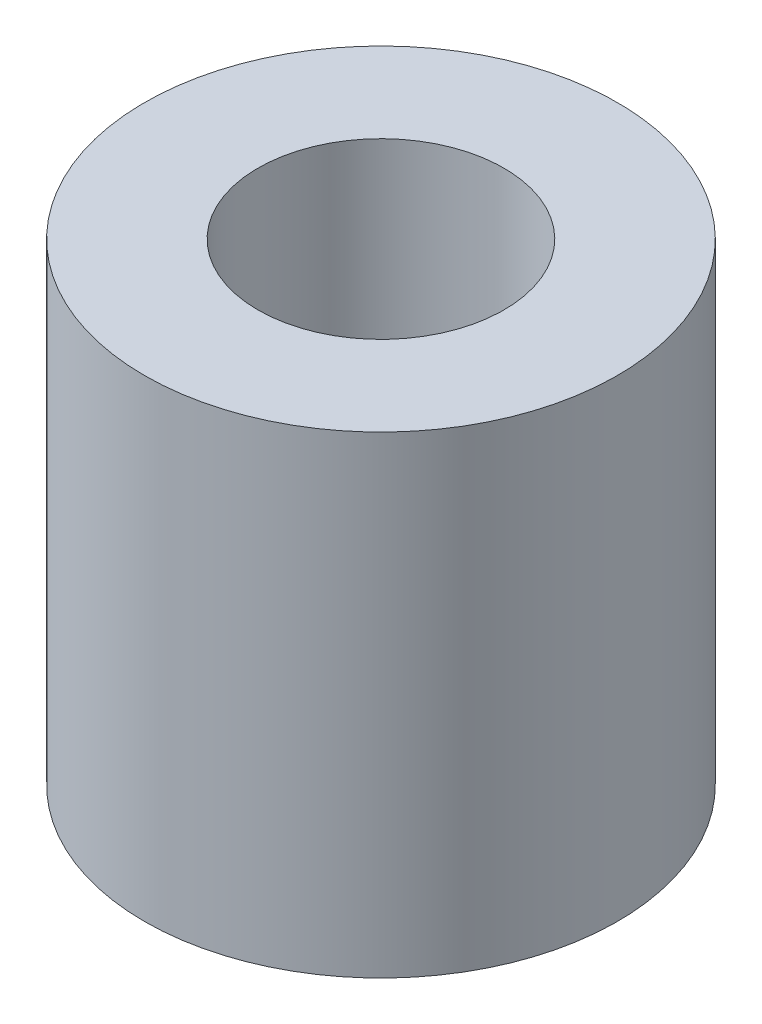
SolidWorks part; units mm, degrees
ref_plane "Front" through (0, 0, 0) normal (0, 0, 1) x (1, 0, 0)
ref_plane "Top" through (0, 0, 0) normal (0, 1, 0) x (1, 0, 0)
ref_plane "Right" through (0, 0, 0) normal (1, 0, 0) x (0, 0, -1)
sketch "Sketch1" plane through (0, 0, 0) normal (0, 1, 0) x (1, 0, 0)
  circle A0 centre (0, 0) radius 2.6
  circle A1 centre (0, 0) radius 5
  dimension "D1" = 5.2
  dimension "D2" = 10
extrude "Boss-Extrude1" add sketch "Sketch1" along normal blind 10
